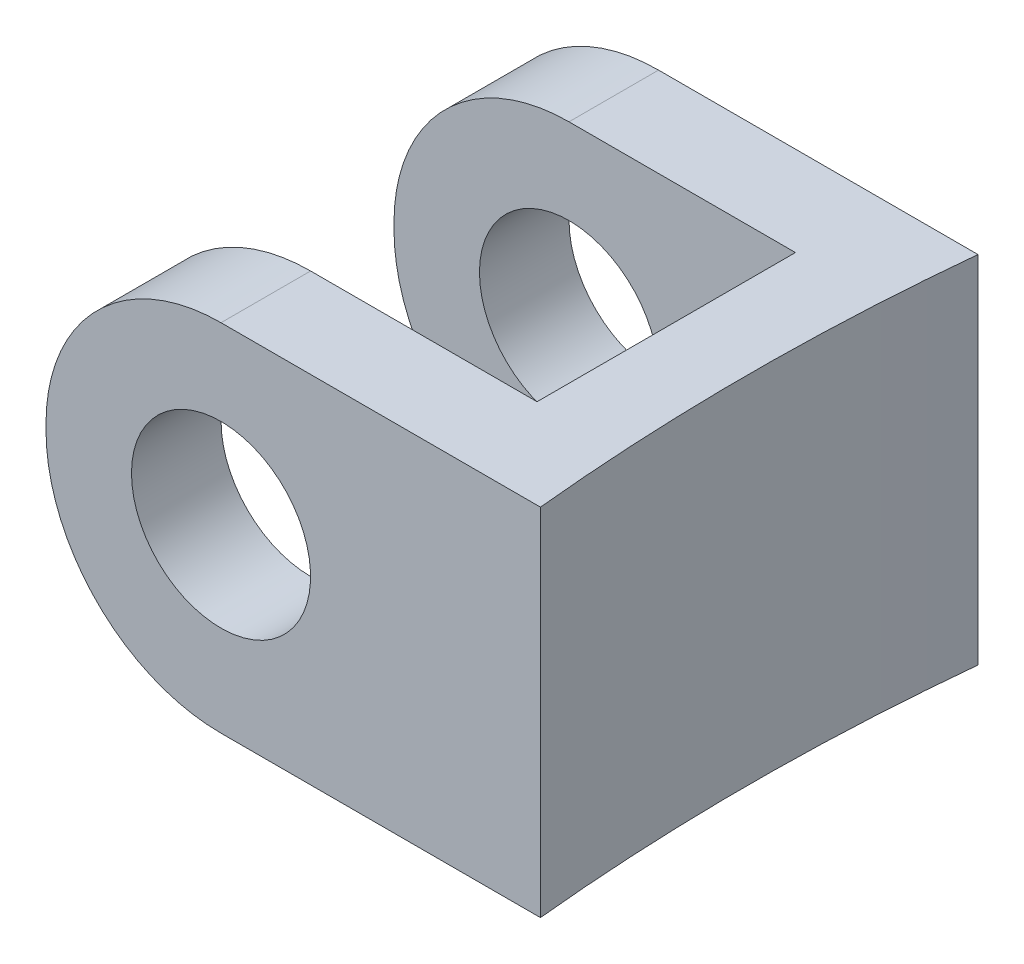
SolidWorks part; units mm, degrees
ref_plane "Front Plane" through (0, 0, 0) normal (0, 0, 1) x (1, 0, 0)
ref_plane "Top Plane" through (0, 0, 0) normal (0, 1, 0) x (1, 0, 0)
ref_plane "Right Plane" through (0, 0, 0) normal (1, 0, 0) x (0, 0, -1)
sketch "Sketch1" plane through (0, 0, 0) normal (0, 1, 0) x (1, 0, 0)
  line L0 (0, 0) -> (11.2268, 0)
  line L1 (0, 0) -> (0, -2.0797)
  line L4 (9.3218, -5.08) -> (9.3218, -2.0797)
  line L5 (9.3218, -2.0797) -> (0, -2.0797)
  line L6 (0, -8.0797) -> (0, -10.16)
  line L7 (9.3218, -5.08) -> (9.3218, -8.0797)
  line L8 (9.3218, -8.0797) -> (0, -8.0797)
  line L9 (0, -10.16) -> (11.2268, -10.16)
  line L12 (11.2268, -10.16) -> (11.4814, -10.16)
  line L13 (11.2268, 0) -> (11.4814, 0)
  arc A0 (11.4814, 0) -> (11.4814, -10.16) centre (62.0268, -5.08) ccw
  dimension "D1" = 11.2268
  dimension "D2" = 10.16
  dimension "D3" = 6
extrude "Boss-Extrude2" add sketch "Sketch1" along normal blind 8.255
fillet "Fillet1" radius 4.064 4 edges at (0, 0, 9.1199) (0, 8.255, 9.1199) (0, 0, 1.0399) (0, 8.255, 1.0399)
sketch "Sketch2" plane through (0, 0, 0) normal (0, 0, -1) x (-1, 0, 0)
  circle A0 centre (-4.064, 4.191) radius 2.079
  dimension "D2" = 4.158
extrude "Cut-Extrude1" cut sketch "Sketch2" against normal through all
